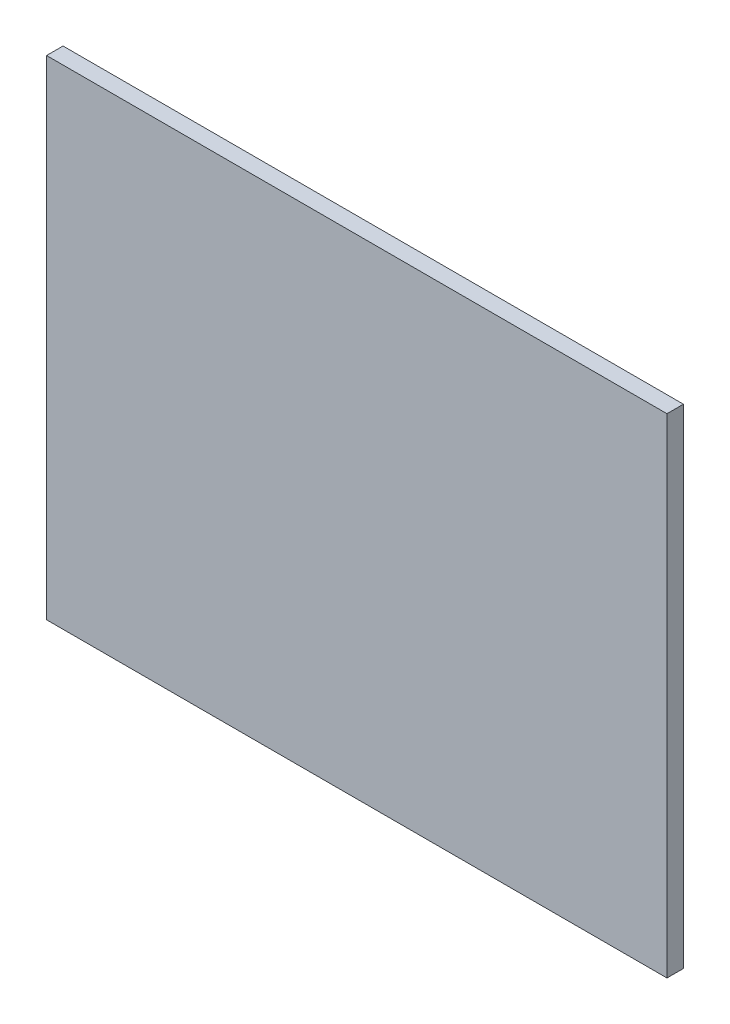
SolidWorks part; units mm, degrees
ref_plane "Ebene vorne" through (0, 0, 0) normal (0, 0, 1) x (1, 0, 0)
ref_plane "Ebene oben" through (0, 0, 0) normal (0, 1, 0) x (1, 0, 0)
ref_plane "Ebene rechts" through (0, 0, 0) normal (1, 0, 0) x (0, 0, -1)
sketch "Skizze1" plane through (0, 0, 0) normal (0, 0, 1) x (1, 0, 0)
  line L1 (301.5, -237.5) -> (-301.5, -237.5)
  line L2 (301.5, -237.5) -> (301.5, 237.5)
  line L3 (301.5, 237.5) -> (-301.5, 237.5)
  line L4 (-301.5, -237.5) -> (-301.5, 237.5)
  line L5 (301.5, -237.5) -> (-301.5, 237.5) construction
  line L6 (301.5, 237.5) -> (-301.5, -237.5) construction
  point P0 (0, 0)
  dimension "D1" = 603
  dimension "D2" = 475
extrude "Aufsatz-Linear austragen1" add sketch "Skizze1" along normal blind 16
